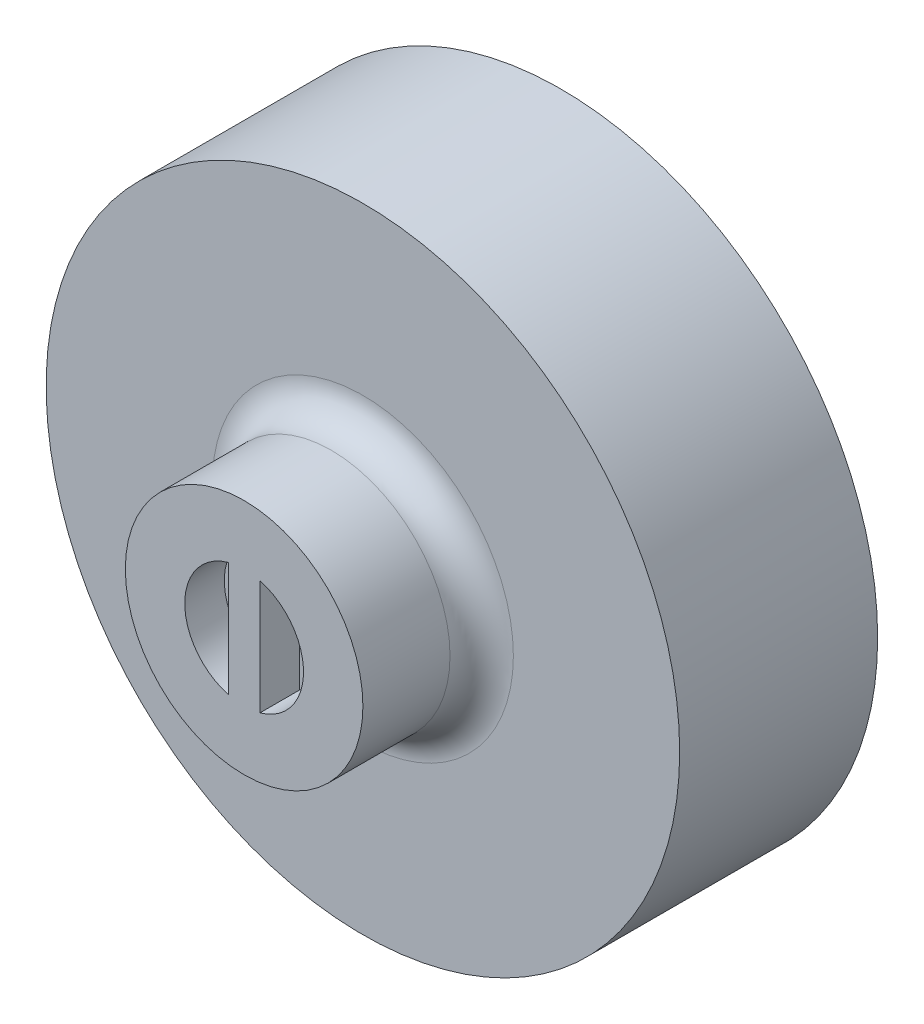
SolidWorks part; units mm, degrees
material "Plain Carbon Steel"
ref_plane "Front Plane" through (0, 0, 0) normal (0, 0, 1) x (1, 0, 0)
ref_plane "Top Plane" through (0, 0, 0) normal (0, 1, 0) x (1, 0, 0)
ref_plane "Right Plane" through (0, 0, 0) normal (1, 0, 0) x (0, 0, -1)
sketch "Sketch1" plane through (0, 0, 0) normal (0, 0, 1) x (1, 0, 0)
  circle A0 centre (0, 0) radius 25.4
  dimension "D1" = 50.8
extrude "Boss-Extrude1" add sketch "Sketch1" against normal blind 15.875
sketch "Sketch2" plane through (0, 0, 0) normal (0, 0, 1) x (1, 0, 0)
  circle A0 centre (0, 0) radius 9.525
  dimension "D1" = 19.05
extrude "Boss-Extrude2" add sketch "Sketch2" along normal blind 9.525
fillet "Fillet2" radius 2.54 1 edges at (9.525, 0, 0)
sketch "Sketch3" plane through (0, 0, 9.525) normal (0, 0, 1) x (1, 0, 0)
  line L1 (-1.27, 4.59) -> (-1.27, -4.59)
  line L2 (1.27, 4.59) -> (1.27, -4.59)
  arc A0 (-1.27, 4.59) -> (-1.27, -4.59) centre (0, 0) ccw
  arc A1 (1.27, -4.59) -> (1.27, 4.59) centre (0, 0) ccw
  dimension "D1" = 9.525
extrude "Cut-Extrude1" cut sketch "Sketch3" against normal blind 3.175
